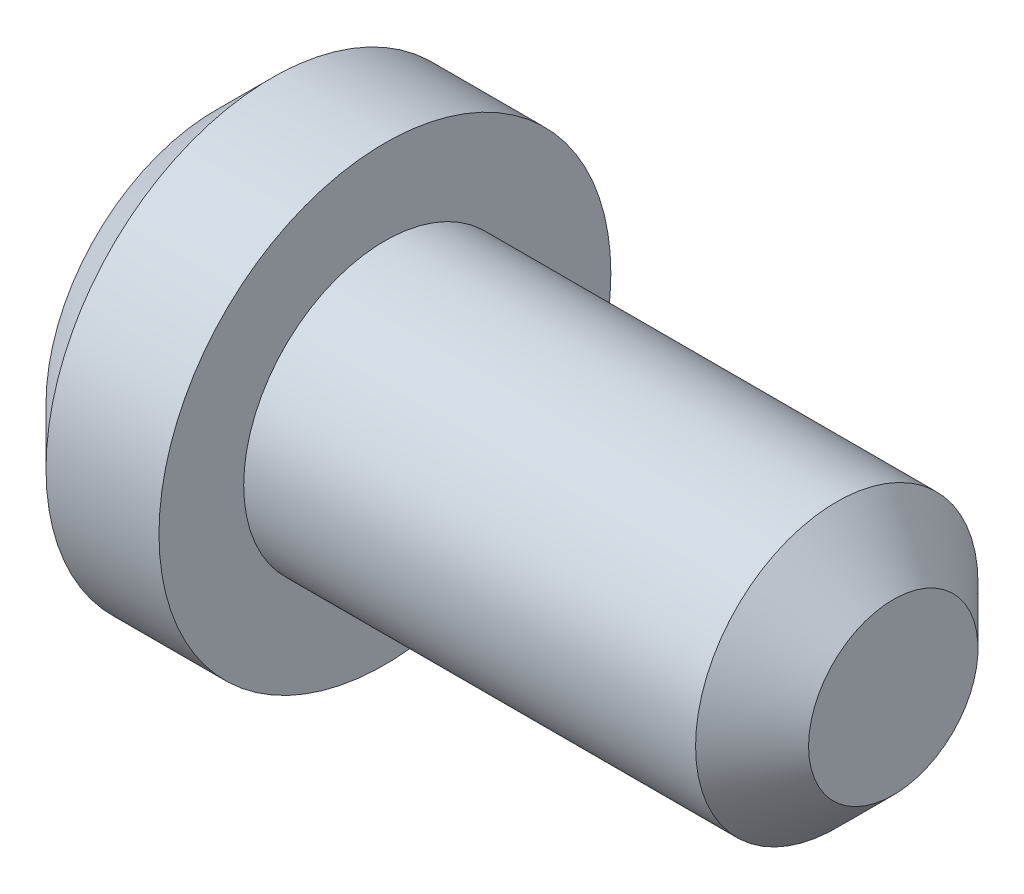
SolidWorks part; units mm, degrees
ref_plane "Front Plane" through (0, 0, 0) normal (0, 0, 1) x (1, 0, 0)
ref_plane "Top Plane" through (0, 0, 0) normal (0, 1, 0) x (1, 0, 0)
ref_plane "Right Plane" through (0, 0, 0) normal (1, 0, 0) x (0, 0, -1)
sketch "Sketch1" plane through (0, 0, 0) normal (0, 0, 1) x (1, 0, 0)
  line L0 (0, 40) -> (20, 40)
  line L1 (-10, 0) -> (110, 0)
  line L2 (0, 40) -> (-10, 30)
  line L3 (110, 0) -> (110, 15)
  line L4 (20, 25) -> (20, 40)
  line L5 (-10, 30) -> (-10, 0)
  line L6 (100, 25) -> (110, 15)
  line L10 (20, 25) -> (100, 25)
  point P4 (110, 25)
  point P5 (-10, 40)
  point P13 (104, 25)
  dimension "D1" = 10
  dimension "D2" = 10
  dimension "D3" = 45
  dimension "D5" = 45
revolve "Revolve1" add sketch "Sketch1" angle 360 about L1
